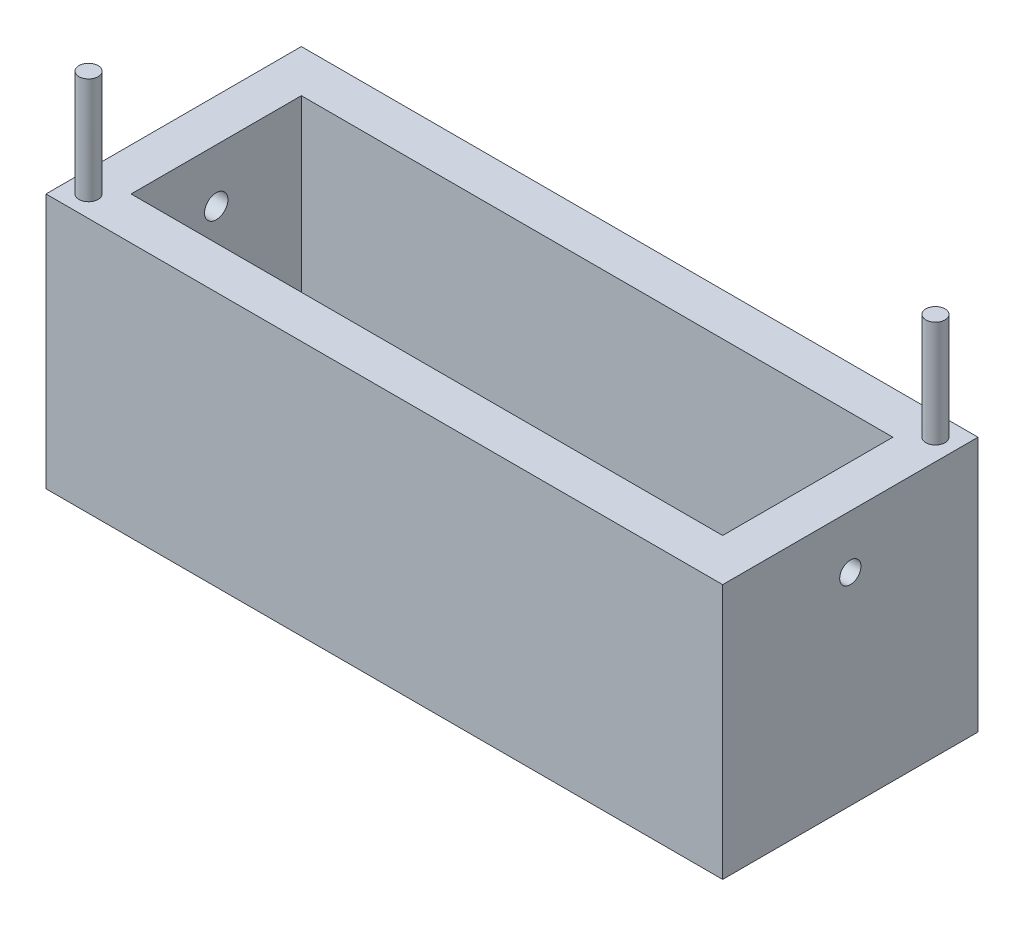
SolidWorks part; units mm, degrees
ref_plane "Front Plane" through (0, 0, 0) normal (0, 0, 1) x (1, 0, 0)
ref_plane "Top Plane" through (0, 0, 0) normal (0, 1, 0) x (1, 0, 0)
ref_plane "Right Plane" through (0, 0, 0) normal (1, 0, 0) x (0, 0, -1)
sketch "Sketch1" plane through (0, 0, 0) normal (0, 1, 0) x (1, 0, 0)
  line L1 (0, 0) -> (403.86, 0)
  line L2 (0, 0) -> (0, 152.4)
  line L3 (0, 152.4) -> (403.86, 152.4)
  line L4 (403.86, 0) -> (403.86, 152.4)
  dimension "D1" = 152.4
  dimension "D2" = 403.86
extrude "Boss-Extrude1" add sketch "Sketch1" along normal blind 152.4
sketch "Sketch3" plane through (0, 152.4, 0) normal (0, 1, 0) x (1, 0, 0)
  line L0 (0, 76.2) -> (25.4, 76.2) construction
  line L1 (0, 152.4) -> (0, 0) construction
  line L2 (403.86, 76.2) -> (378.46, 76.2) construction
  line L3 (403.86, 0) -> (403.86, 152.4) construction
  line L4 (201.93, 152.4) -> (201.93, 127) construction
  line L5 (403.86, 152.4) -> (0, 152.4) construction
  line L6 (201.93, 0) -> (201.93, 25.4) construction
  line L7 (0, 0) -> (403.86, 0) construction
  line L9 (25.4, 127) -> (378.46, 127)
  line L10 (25.4, 127) -> (25.4, 25.4)
  line L11 (25.4, 25.4) -> (378.46, 25.4)
  line L12 (378.46, 127) -> (378.46, 25.4)
  dimension "D1" = 25.4
  dimension "D2" = 353.06
extrude "Cut-Extrude1" cut sketch "Sketch3" against normal blind 139.7
sketch "Sketch11" plane through (0, 152.4, 0) normal (0, 1, 0) x (1, 0, 0)
  line L0 (25.4, 127) -> (25.4, 25.4) construction
  line L3 (0, 0) -> (403.86, 0) construction
  circle A0 centre (12.7, 12.7) radius 5.715
  dimension "D1" = 12.7
  dimension "D3" = 11.43
  dimension "D2" = 12.7
sketch "Sketch13" plane through (0, 152.4, 0) normal (0, 1, 0) x (1, 0, 0)
  line L0 (378.46, 25.4) -> (378.46, 127) construction
  line L1 (378.46, 127) -> (25.4, 127) construction
  circle A0 centre (391.16, 139.7) radius 5.715
  dimension "D1" = 12.7
  dimension "D3" = 11.43
  dimension "D2" = 12.7
extrude "Boss-Extrude3" add sketch "Sketch11" along normal blind 63.5 contours A0
extrude "Boss-Extrude4" add sketch "Sketch13" along normal blind 63.5
sketch "Sketch15" plane through (403.86, 0, 0) normal (1, 0, 0) x (0, 0, -1)
  line L0 (0, 152.4) -> (152.4, 152.4) construction
  line L1 (0, 152.4) -> (0, 0) construction
  circle A0 centre (76.2, 120.65) radius 6.35
  dimension "D1" = 31.75
  dimension "D2" = 76.2
extrude "Cut-Extrude2" cut sketch "Sketch15" against normal blind 63.5 contours A0
sketch "Sketch16" plane through (0, 0, 0) normal (-1, 0, 0) x (0, 0, 1)
  line L0 (-152.4, 152.4) -> (0, 152.4) construction
  line L1 (-152.4, 152.4) -> (-152.4, 0) construction
  circle A0 centre (-76.2, 120.65) radius 6.985
  dimension "D1" = 31.75
  dimension "D2" = 76.2
  dimension "D3" = 13.97
extrude "Cut-Extrude3" cut sketch "Sketch16" against normal blind 63.5
